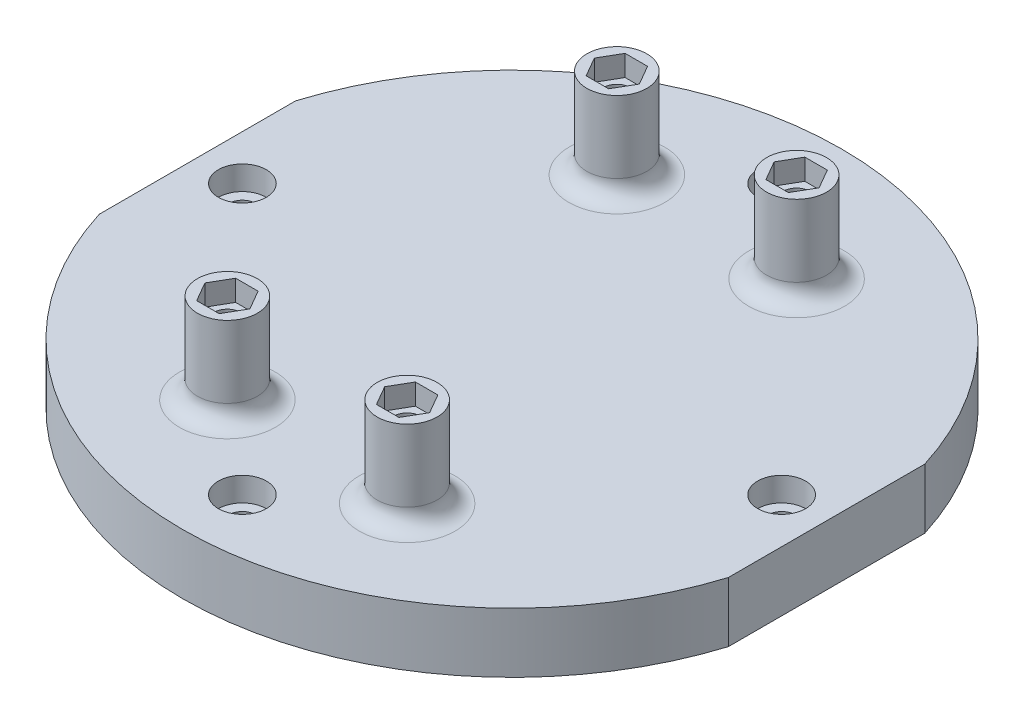
SolidWorks part; units mm, degrees
ref_plane "Front Plane" through (0, 0, 0) normal (0, 0, 1) x (1, 0, 0)
ref_plane "Top Plane" through (0, 0, 0) normal (0, 1, 0) x (1, 0, 0)
ref_plane "Right Plane" through (0, 0, 0) normal (1, 0, 0) x (0, 0, -1)
sketch "Sketch1" plane through (0, 0, 0) normal (0, 1, 0) x (1, 0, 0)
  line L2 (-52.5, -16.3936) -> (-52.5, 16.3936)
  line L4 (52.5, -16.3936) -> (52.5, 16.3936)
  line L5 (-52.5, -65) -> (52.5, 65) construction
  line L6 (-52.5, 65) -> (52.5, -65) construction
  arc A0 (-52.5, -16.3936) -> (52.5, -16.3936) centre (0, 0) ccw
  arc A1 (52.5, 16.3936) -> (-52.5, 16.3936) centre (0, 0) ccw
  dimension "D1" = 110
  dimension "D2" = 105
  dimension "D3" = 130
extrude "Boss-Extrude1" add sketch "Sketch1" along normal blind 10
sketch "Screw locations" plane through (0, 10, 0) normal (0, 1, 0) x (1, 0, 0)
  line L1 (-15, -32.5) -> (15, -32.5) construction
  line L2 (-15, -32.5) -> (-15, 32.5) construction
  line L3 (-15, 32.5) -> (15, 32.5) construction
  line L4 (15, -32.5) -> (15, 32.5) construction
  line L5 (-15, -32.5) -> (15, 32.5) construction
  line L6 (-15, 32.5) -> (15, -32.5) construction
  circle A0 centre (0, 0) radius 45 construction
  point P3 (0, 45)
  point P4 (-45, 0)
  point P5 (0, -45)
  point P6 (45, 0)
  dimension "D1" = 90
  dimension "D2" = 32.5
  dimension "D3" = 15
hole_wizard "CBORE for M4 SHCS1" positions "Sketch3" profile "Sketch4" counterbore size "M4" standard "ANSI Metric" end condition through all
sketch "Sketch3" plane through (0, 10, 0) normal (0, 1, 0) x (1, 0, 0)
  point P0 (-45, 0)
  point P3 (0, 45)
  point P6 (45, 0)
  point P9 (0, -45)
sketch "Sketch4" plane through (-45, 10, 0) normal (1, 0, 0) x (0, 0, 1)
  line L0 (0, 0) -> (0, 10)
  line L1 (0, 10) -> (2.25, 10)
  line L3 (2.25, 10) -> (2.25, 4)
  line L4 (2.25, 4) -> (4, 4)
  line L5 (4, 4) -> (4, 0)
  line L7 (4, 0) -> (0, 0)
  line L11 (0, -6.35) -> (0, 107.95) construction
  dimension "Thru Hole Dia." = 4.5
  dimension "Thru Hole Depth" = 10
  dimension "C'Bore Dia." = 8
  dimension "C'Bore Depth" = 4
hole_wizard "CBORE for M4 SHCS2" positions "Sketch5" profile "Sketch6" counterbore size "M4" standard "ANSI Metric" end condition through all
sketch "Sketch5" plane through (0, 0, 0) normal (0, -1, 0) x (-1, 0, 0)
  point P0 (15, -32.5)
  point P3 (-15, -32.5)
  point P6 (15, 32.5)
  point P9 (-15, 32.5)
sketch "Sketch6" plane through (-15, 0, 32.5) normal (1, 0, 0) x (0, 0, -1)
  line L0 (0, 0) -> (0, 10)
  line L1 (0, 10) -> (2.25, 10)
  line L3 (2.25, 10) -> (2.25, 4)
  line L4 (2.25, 4) -> (4, 4)
  line L5 (4, 4) -> (4, 0)
  line L7 (4, 0) -> (0, 0)
  line L11 (0, -6.35) -> (0, 107.95) construction
  dimension "Thru Hole Dia." = 4.5
  dimension "Thru Hole Depth" = 10
  dimension "C'Bore Dia." = 8
  dimension "C'Bore Depth" = 4
sketch "Sketch8" plane through (0, 10, 0) normal (0, 1, 0) x (1, 0, 0)
  line L0 (0, 0) -> (0, 20.698) construction
  line L1 (-11.2472, 32.5) -> (-13.1236, 35.75)
  line L2 (-13.1236, 35.75) -> (-16.8764, 35.75)
  line L3 (-16.8764, 35.75) -> (-18.7528, 32.5)
  line L4 (-18.7528, 32.5) -> (-16.8764, 29.25)
  line L5 (-16.8764, 29.25) -> (-13.1236, 29.25)
  line L6 (-13.1236, 29.25) -> (-11.2472, 32.5)
  line L7 (0, 0) -> (21.8634, 0) construction
  line L8 (13.1236, 29.25) -> (11.2472, 32.5)
  line L9 (16.8764, 29.25) -> (13.1236, 29.25)
  line L10 (18.7528, 32.5) -> (16.8764, 29.25)
  line L11 (16.8764, 35.75) -> (18.7528, 32.5)
  line L12 (13.1236, 35.75) -> (16.8764, 35.75)
  line L13 (11.2472, 32.5) -> (13.1236, 35.75)
  line L14 (16.8764, -29.25) -> (13.1236, -29.25)
  line L15 (18.7528, -32.5) -> (16.8764, -29.25)
  line L16 (16.8764, -35.75) -> (18.7528, -32.5)
  line L17 (13.1236, -35.75) -> (16.8764, -35.75)
  line L18 (11.2472, -32.5) -> (13.1236, -35.75)
  line L19 (13.1236, -29.25) -> (11.2472, -32.5)
  line L20 (-13.1236, -29.25) -> (-11.2472, -32.5)
  line L21 (-16.8764, -29.25) -> (-13.1236, -29.25)
  line L22 (-18.7528, -32.5) -> (-16.8764, -29.25)
  line L23 (-16.8764, -35.75) -> (-18.7528, -32.5)
  line L24 (-13.1236, -35.75) -> (-16.8764, -35.75)
  line L25 (-11.2472, -32.5) -> (-13.1236, -35.75)
  circle A0 centre (-15, 32.5) radius 3.25 construction
  circle A1 centre (-15, 32.5) radius 5
  circle A2 centre (15, 32.5) radius 5
  circle A3 centre (-15, -32.5) radius 5
  circle A4 centre (15, -32.5) radius 5
  dimension "D2" = 10
  dimension "D1" = 6.5
extrude "Boss-Extrude2" add sketch "Sketch8" along normal blind 15
fillet "Fillet1" radius 3 4 edges at (-15, 10, 27.5) (15, 10, 37.5) (15, 10, -37.5) (-15, 10, -27.5)
sketch "Sketch10" plane through (0, 10, 0) normal (0, 1, 0) x (1, 0, 0)
  line L0 (0, 0) -> (0, 14.7713) construction
  line L1 (-13.1236, 35.75) -> (-16.8764, 35.75)
  line L2 (-16.8764, 35.75) -> (-18.7528, 32.5)
  line L3 (-18.7528, 32.5) -> (-16.8764, 29.25)
  line L4 (-16.8764, 29.25) -> (-13.1236, 29.25)
  line L5 (-13.1236, 29.25) -> (-11.2472, 32.5)
  line L6 (-11.2472, 32.5) -> (-13.1236, 35.75)
  line L7 (0, 14.7713) -> (0, 0) construction
  line L8 (0, 0) -> (16.507, 0) construction
  line L9 (11.2472, 32.5) -> (13.1236, 35.75)
  line L10 (13.1236, 29.25) -> (11.2472, 32.5)
  line L11 (16.8764, 29.25) -> (13.1236, 29.25)
  line L12 (18.7528, 32.5) -> (16.8764, 29.25)
  line L13 (16.8764, 35.75) -> (18.7528, 32.5)
  line L14 (13.1236, 35.75) -> (16.8764, 35.75)
  line L15 (13.1236, -29.25) -> (11.2472, -32.5)
  line L16 (16.8764, -29.25) -> (13.1236, -29.25)
  line L17 (18.7528, -32.5) -> (16.8764, -29.25)
  line L18 (16.8764, -35.75) -> (18.7528, -32.5)
  line L19 (13.1236, -35.75) -> (16.8764, -35.75)
  line L20 (11.2472, -32.5) -> (13.1236, -35.75)
  line L21 (-11.2472, -32.5) -> (-13.1236, -35.75)
  line L22 (-13.1236, -29.25) -> (-11.2472, -32.5)
  line L23 (-16.8764, -29.25) -> (-13.1236, -29.25)
  line L24 (-18.7528, -32.5) -> (-16.8764, -29.25)
  line L25 (-16.8764, -35.75) -> (-18.7528, -32.5)
  line L26 (-13.1236, -35.75) -> (-16.8764, -35.75)
  circle A0 centre (-15, 32.5) radius 3.25 construction
  circle A1 centre (-15, 32.5) radius 2.25
  circle A2 centre (15, 32.5) radius 2.25
  circle A3 centre (15, 32.5) radius 3.25 construction
  circle A4 centre (15, -32.5) radius 2.25
  circle A5 centre (-15, -32.5) radius 2.25
  dimension "D1" = 6.5
extrude "Boss-Extrude3" add sketch "Sketch10" along normal blind 11.5
